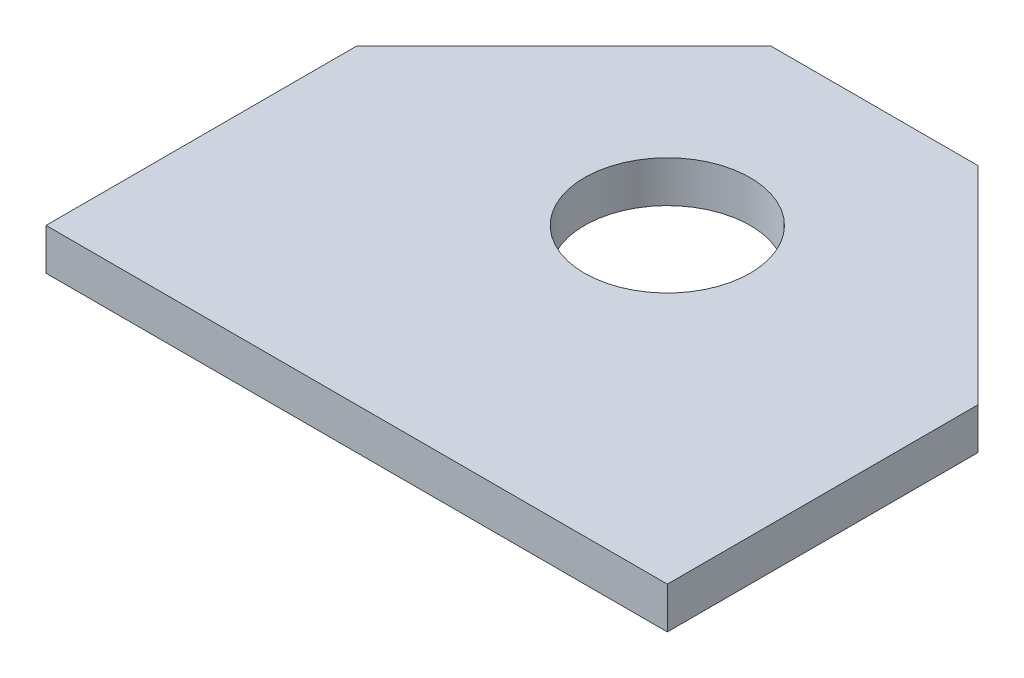
SolidWorks part; units mm, degrees
ref_plane "Front Plane" through (0, 0, 0) normal (0, 0, 1) x (1, 0, 0)
ref_plane "Top Plane" through (0, 0, 0) normal (0, 1, 0) x (1, 0, 0)
ref_plane "Right Plane" through (0, 0, 0) normal (1, 0, 0) x (0, 0, -1)
sketch "Sketch1" plane through (0, 0, 0) normal (0, 1, 0) x (1, 0, 0)
  line L0 (0, 10) -> (0, -15) construction
  line L1 (5, 10) -> (-5, 10)
  line L2 (-5, 10) -> (-15, 0)
  line L3 (-15, 0) -> (-15, -15)
  line L4 (-15, -15) -> (15, -15)
  line L5 (15, 0) -> (15, -15)
  line L6 (5, 10) -> (15, 0)
  circle A0 centre (0, 0) radius 4
  dimension "D3" = 8
  dimension "D1" = 45
  dimension "D2" = 30
  dimension "D4" = 15
  dimension "D5" = 10
extrude "Boss-Extrude1" add sketch "Sketch1" along normal mid plane 2
